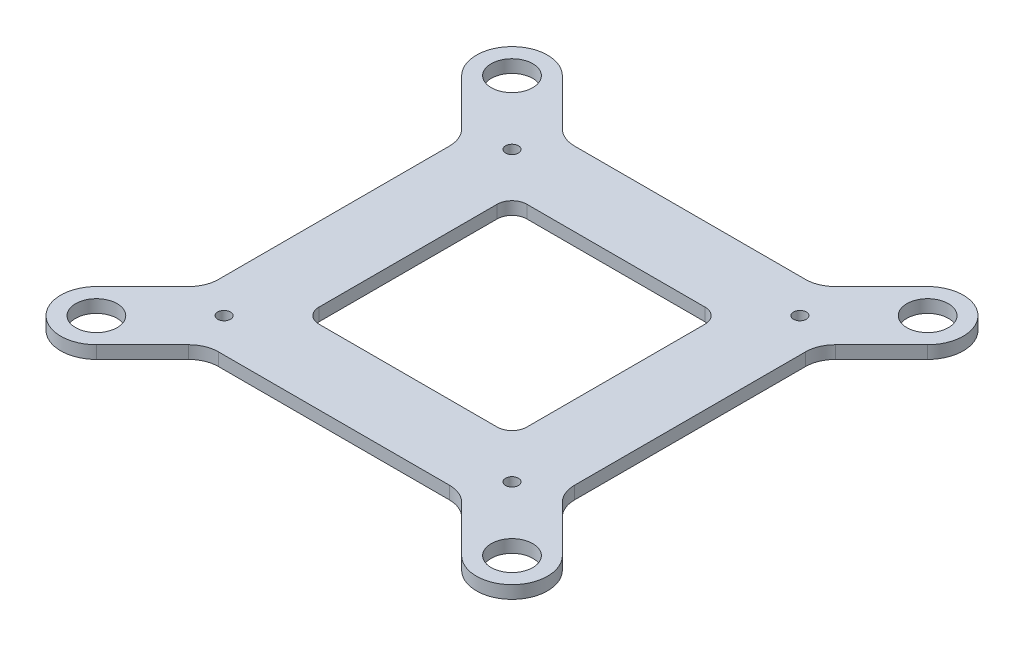
SolidWorks part; units mm, degrees
material "ABS"
ref_plane "Front Plane" through (0, 0, 0) normal (0, 0, 1) x (1, 0, 0)
ref_plane "Top Plane" through (0, 0, 0) normal (0, 1, 0) x (1, 0, 0)
ref_plane "Right Plane" through (0, 0, 0) normal (1, 0, 0) x (0, 0, -1)
sketch "Sketch1" plane through (0, 0, 0) normal (0, 1, 0) x (1, 0, 0)
  line L0 (-30, 19.4437) -> (-30, -19.4437)
  line L1 (-24.245, -24.245) -> (24.245, -24.245) construction
  line L2 (-24.245, -24.245) -> (-24.245, 24.245) construction
  line L3 (-24.245, 24.245) -> (24.245, 24.245) construction
  line L4 (24.245, -24.245) -> (24.245, 24.245) construction
  line L5 (-24.245, -24.245) -> (24.245, 24.245) construction
  line L6 (-24.245, 24.245) -> (24.245, -24.245) construction
  line L7 (-19.4437, 30) -> (19.4437, 30)
  line L8 (30, 19.4437) -> (30, -19.4437)
  line L9 (-19.4437, -30) -> (19.4437, -30)
  line L10 (39.2426, -30.7574) -> (31.4645, -22.9792)
  line L11 (-15, -17.5) -> (15, -17.5)
  line L12 (-17.5, -15) -> (-17.5, 15)
  line L13 (-15, 17.5) -> (15, 17.5)
  line L14 (17.5, -15) -> (17.5, 15)
  line L15 (-17.5, -17.5) -> (17.5, 17.5) construction
  line L16 (-17.5, 17.5) -> (17.5, -17.5) construction
  line L17 (35, 35) -> (-35, 35) construction
  line L18 (35, 35) -> (35, -35) construction
  line L19 (35, -35) -> (-35, -35) construction
  line L20 (-35, 35) -> (-35, -35) construction
  line L21 (35, 35) -> (-35, -35) construction
  line L22 (35, -35) -> (-35, 35) construction
  line L23 (30.7574, -39.2426) -> (22.9792, -31.4645)
  line L24 (-30.7574, -39.2426) -> (-22.9792, -31.4645)
  line L25 (-39.2426, -30.7574) -> (-31.4645, -22.9792)
  line L26 (-39.2426, 30.7574) -> (-31.4645, 22.9792)
  line L27 (-30.7574, 39.2426) -> (-22.9792, 31.4645)
  line L28 (30.7574, 39.2426) -> (22.9792, 31.4645)
  line L29 (39.2426, 30.7574) -> (31.4645, 22.9792)
  circle A0 centre (-24.245, 24.245) radius 1.075
  circle A1 centre (24.245, 24.245) radius 1.075
  circle A2 centre (24.245, -24.245) radius 1.075
  circle A3 centre (-24.245, -24.245) radius 1.075
  arc A8 (15, -17.5) -> (17.5, -15) centre (15, -15) ccw
  arc A9 (-15, -17.5) -> (-17.5, -15) centre (-15, -15) cw
  arc A10 (15, 17.5) -> (17.5, 15) centre (15, 15) cw
  arc A11 (-17.5, 15) -> (-15, 17.5) centre (-15, 15) cw
  circle A13 centre (35, -35) radius 3.5
  circle A28 centre (-35, -35) radius 3.5
  arc A29 (30.7574, -39.2426) -> (39.2426, -30.7574) centre (35, -35) ccw
  arc A30 (-39.2426, -30.7574) -> (-30.7574, -39.2426) centre (-35, -35) ccw
  circle A31 centre (-35, 35) radius 3.5
  arc A32 (-30.7574, 39.2426) -> (-39.2426, 30.7574) centre (-35, 35) ccw
  circle A33 centre (35, 35) radius 3.5
  arc A34 (39.2426, 30.7574) -> (30.7574, 39.2426) centre (35, 35) ccw
  arc A35 (31.4645, -22.9792) -> (30, -19.4437) centre (35, -19.4437) cw
  arc A36 (31.4645, 22.9792) -> (30, 19.4437) centre (35, 19.4437) ccw
  arc A37 (22.9792, 31.4645) -> (19.4437, 30) centre (19.4437, 35) cw
  arc A38 (-22.9792, 31.4645) -> (-19.4437, 30) centre (-19.4437, 35) ccw
  arc A39 (-31.4645, 22.9792) -> (-30, 19.4437) centre (-35, 19.4437) cw
  arc A40 (-31.4645, -22.9792) -> (-30, -19.4437) centre (-35, -19.4437) ccw
  arc A41 (-22.9792, -31.4645) -> (-19.4437, -30) centre (-19.4437, -35) cw
  arc A42 (22.9792, -31.4645) -> (19.4437, -30) centre (19.4437, -35) ccw
  point P0 (0, 0)
  point P10 (0, 0)
  point P15 (0, 0)
  point P16 (0, 0)
  point P17 (-14.2607, -14.2607)
  point P21 (0, 0)
  point P40 (0, 0)
  point P51 (0, 0)
  point P75 (0, 0)
  dimension "D2" = 2.15
  dimension "D3" = 30
  dimension "D5" = 2.5
  dimension "D6" = 7
  dimension "D9" = 2.5
  dimension "D10" = 5
  dimension "D1" = 48.49
  dimension "D4" = 12.5
  dimension "D7" = 35
  dimension "D8" = 4
extrude "Boss-Extrude1" add sketch "Sketch1" along normal blind 2.15
sketch "Sketch2" plane through (0, 0, 0) normal (0, -1, 0) x (1, 0, 0)
  line L0 (27.32, -24.245) -> (27.32, -14.245)
  line L1 (-24.245, -27.32) -> (-14.245, -27.32)
  line L2 (24.245, -27.32) -> (14.245, -27.32)
  line L3 (-27.32, -24.245) -> (-27.32, -14.245)
  line L4 (14.245, -21.17) -> (18.67, -21.17)
  line L5 (21.17, -18.67) -> (21.17, -14.245)
  line L6 (-21.17, -14.245) -> (-21.17, -18.67)
  line L7 (-18.67, -21.17) -> (-14.245, -21.17)
  line L8 (-27.32, 24.245) -> (-27.32, 14.245)
  line L9 (-24.245, 27.32) -> (-14.245, 27.32)
  line L10 (-14.245, 21.17) -> (-18.67, 21.17)
  line L11 (-21.17, 18.67) -> (-21.17, 14.245)
  line L12 (24.245, 27.32) -> (14.245, 27.32)
  line L13 (27.32, 24.245) -> (27.32, 14.245)
  line L14 (21.17, 14.245) -> (21.17, 18.67)
  line L15 (18.67, 21.17) -> (14.245, 21.17)
  arc A0 (24.245, -27.32) -> (27.32, -24.245) centre (24.245, -24.245) ccw
  circle A7 centre (24.245, -24.245) radius 1.075 construction
  circle A11 centre (24.245, -24.245) radius 1.075
  arc A12 (27.32, -14.245) -> (21.17, -14.245) centre (24.245, -14.245) ccw
  arc A13 (14.245, -21.17) -> (14.245, -27.32) centre (14.245, -24.245) ccw
  arc A14 (18.67, -21.17) -> (21.17, -18.67) centre (18.67, -18.67) ccw
  arc A15 (-27.32, -24.245) -> (-24.245, -27.32) centre (-24.245, -24.245) ccw
  circle A16 centre (-24.245, -24.245) radius 1.075
  arc A17 (-14.245, -27.32) -> (-14.245, -21.17) centre (-14.245, -24.245) ccw
  arc A18 (-21.17, -14.245) -> (-27.32, -14.245) centre (-24.245, -14.245) ccw
  arc A19 (-21.17, -18.67) -> (-18.67, -21.17) centre (-18.67, -18.67) ccw
  arc A20 (-24.245, 27.32) -> (-27.32, 24.245) centre (-24.245, 24.245) ccw
  circle A21 centre (-24.245, 24.245) radius 1.075
  arc A22 (-27.32, 14.245) -> (-21.17, 14.245) centre (-24.245, 14.245) ccw
  arc A23 (-14.245, 21.17) -> (-14.245, 27.32) centre (-14.245, 24.245) ccw
  arc A24 (-18.67, 21.17) -> (-21.17, 18.67) centre (-18.67, 18.67) ccw
  arc A25 (27.32, 24.245) -> (24.245, 27.32) centre (24.245, 24.245) ccw
  circle A26 centre (24.245, 24.245) radius 1.075
  arc A27 (14.245, 27.32) -> (14.245, 21.17) centre (14.245, 24.245) ccw
  arc A28 (21.17, 14.245) -> (27.32, 14.245) centre (24.245, 14.245) ccw
  arc A29 (21.17, 18.67) -> (18.67, 21.17) centre (18.67, 18.67) ccw
  circle A30 centre (-24.245, -24.245) radius 1.075 construction
  point P3 (0, 0)
  point P4 (0, 0)
  dimension "D1" = 6.15
  dimension "D2" = 10
  dimension "D3" = 2.5
  dimension "D4" = 4
extrude "Boss-Extrude2" add sketch "Sketch2" along normal blind 2.5
